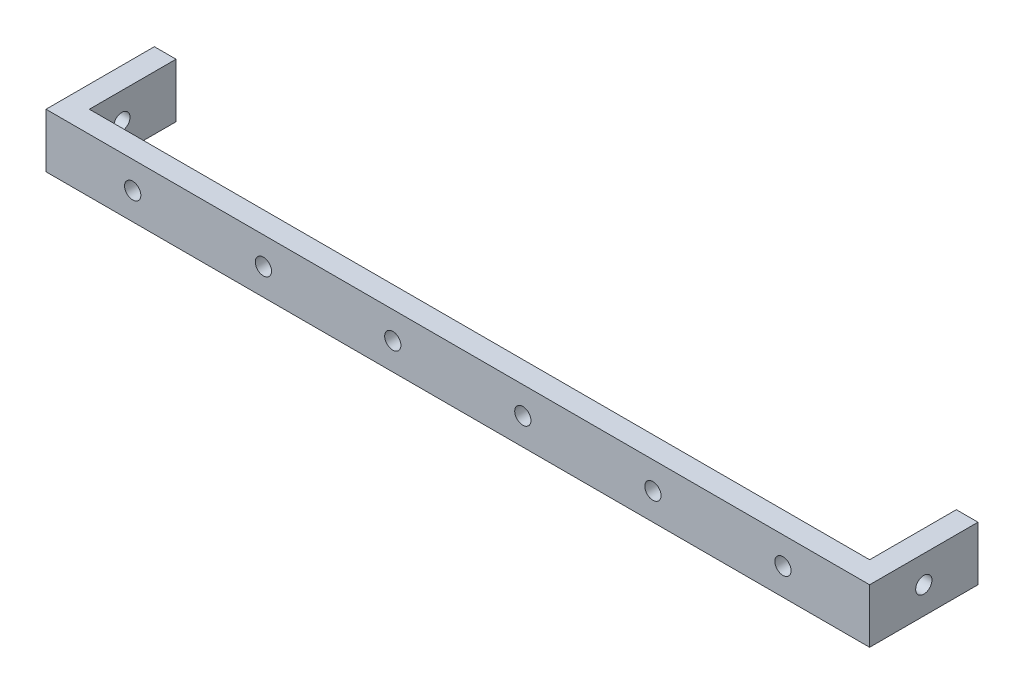
SolidWorks part; units mm, degrees
ref_plane "Front Plane" through (0, 0, 0) normal (0, 0, 1) x (1, 0, 0)
ref_plane "Top Plane" through (0, 0, 0) normal (0, 1, 0) x (1, 0, 0)
ref_plane "Right Plane" through (0, 0, 0) normal (1, 0, 0) x (0, 0, -1)
sketch "Sketch1" plane through (0, 0, 0) normal (0, 0, 1) x (1, 0, 0)
  line L0 (0, 0) -> (36, 0) construction
  line L1 (0, 0) -> (72, 0)
  line L2 (0, 0) -> (0, 5)
  line L3 (0, 5) -> (72, 5)
  line L4 (72, 0) -> (72, 5)
  line L5 (36, 0) -> (36, 18.4023) construction
sketch "Sketch3" plane through (0, 0, 0) normal (0, 0, 1) x (1, 0, 0)
  line L0 (36, 0) -> (36, 2.5) construction
  line L1 (36, 0) -> (36, 18.4023) construction
  line L2 (36, 2.5) -> (30, 2.5) construction
  line L3 (30, 2.5) -> (18, 2.5) construction
  line L4 (18, 2.5) -> (6, 2.5) construction
  line L5 (36, 2.5) -> (42, 2.5) construction
  line L6 (42, 2.5) -> (54, 2.5) construction
  line L7 (54, 2.5) -> (66, 2.5) construction
  circle A0 centre (42, 2.5) radius 0.75
  circle A1 centre (54, 2.5) radius 0.75
  circle A2 centre (66, 2.5) radius 0.75
  circle A6 centre (30, 2.5) radius 0.75
  circle A7 centre (18.0602, 2.4636) radius 0.75
  circle A8 centre (6, 2.5) radius 0.75
  point P16 (30.4457, 2.5)
  point P20 (6, 2.9152)
extrude "Boss-Extrude1" add sketch "Sketch1" along normal blind 2
extrude "Cut-Extrude2" cut sketch "Sketch3" along normal blind 2
ref_plane "Plane1" through (72, 0, 0) normal (1, 0, 0) x (0, 0, -1)
sketch "Sketch4" plane through (72, 0, 0) normal (1, 0, 0) x (0, 0, -1)
  line L1 (-2, 5) -> (8, 5)
  line L2 (-2, 5) -> (-2, 0)
  line L3 (-2, 0) -> (8, 0)
  line L4 (8, 5) -> (8, 0)
extrude "Boss-Extrude2" add sketch "Sketch4" along normal blind 2
sketch "Sketch5" plane through (72, 0, 0) normal (1, 0, 0) x (0, 0, -1)
  line L0 (-2, 5) -> (-2, 2.5) construction
  line L1 (-2, 5) -> (-2, 0) construction
  line L2 (-2, 2.5) -> (3, 2.5) construction
  circle A0 centre (3, 2.5) radius 0.75
extrude "Cut-Extrude4" cut sketch "Sketch5" along normal blind 2
ref_plane "Plane2" through (0, 0, 0) normal (-1, 0, 0) x (0, 0, 1)
sketch "Sketch6" plane through (0, 0, 0) normal (-1, 0, 0) x (0, 0, 1)
  line L1 (2, 0) -> (-8, 0)
  line L2 (2, 0) -> (2, 5)
  line L3 (2, 5) -> (-8, 5)
  line L4 (-8, 0) -> (-8, 5)
extrude "Boss-Extrude3" add sketch "Sketch6" along normal blind 2
sketch "Sketch7" plane through (0, 0, 0) normal (-1, 0, 0) x (0, 0, 1)
  line L0 (2, 0) -> (2, 2.5) construction
  line L1 (2, 0) -> (2, 5) construction
  line L2 (2, 2.5) -> (-3, 2.5) construction
  circle A0 centre (-3, 2.5) radius 0.75
extrude "Cut-Extrude5" cut sketch "Sketch7" along normal blind 2
